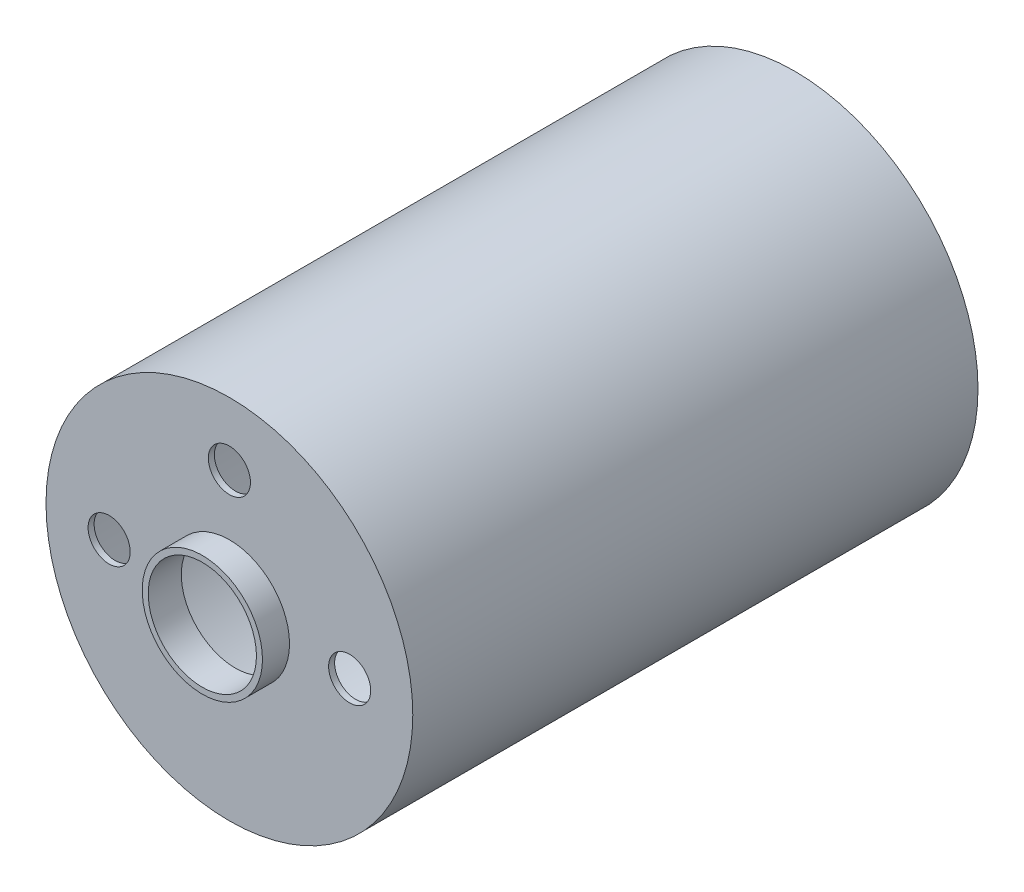
SolidWorks part; units mm, degrees
ref_plane "前视基准面" through (0, 0, 0) normal (0, 0, 1) x (1, 0, 0)
ref_plane "上视基准面" through (0, 0, 0) normal (0, 1, 0) x (1, 0, 0)
ref_plane "右视基准面" through (0, 0, 0) normal (1, 0, 0) x (0, 0, -1)
other "Configuration Table"
sketch "Sketch1" plane through (0, 0, 0) normal (0, 0, 1) x (1, 0, 0)
  circle A0 centre (0, 0) radius 15.25
  dimension "D1" = 30.5
extrude "Boss-Extrude1" add sketch "Sketch1" along normal mid plane 47
sketch "Sketch2" plane through (0, 0, 23.5) normal (0, 0, 1) x (1, 0, 0)
  circle A0 centre (0, 0) radius 5
  dimension "D1" = 10
extrude "Boss-Extrude2" add sketch "Sketch2" along normal mid plane 4.5
shell "Shell1" thickness 0.5
sketch "Sketch3" plane through (0, 0, 23.5) normal (0, 0, 1) x (1, 0, 0)
  circle A0 centre (-10, 0) radius 1.75
  circle A1 centre (0, 10) radius 1.75
  circle A2 centre (10, 0) radius 1.75
  point P10 (0, 0)
  dimension "D1" = 10
  dimension "D2" = 3.5
  dimension "D3" = 3
extrude "Cut-Extrude1" cut sketch "Sketch3" against normal blind 4.5
